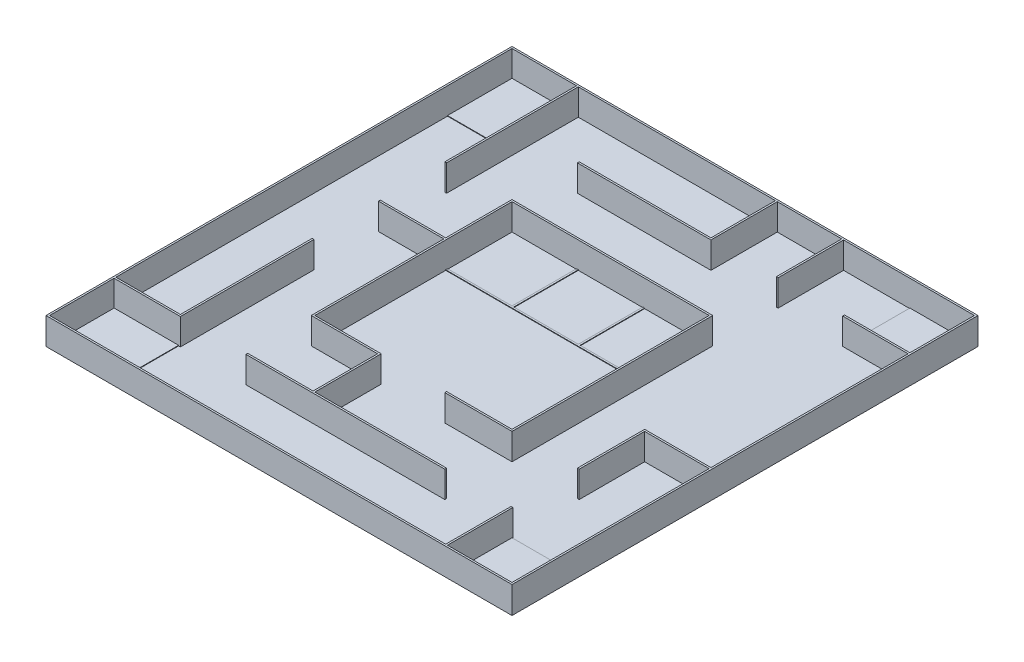
SolidWorks part; units mm, degrees
ref_plane "Front Plane" through (0, 0, 0) normal (0, 0, 1) x (1, 0, 0)
ref_plane "Top Plane" through (0, 0, 0) normal (0, 1, 0) x (1, 0, 0)
ref_plane "Right Plane" through (0, 0, 0) normal (1, 0, 0) x (0, 0, -1)
sketch "Sketch1" plane through (0, 0, 0) normal (0, 1, 0) x (1, 0, 0)
  line L0 (-925, 555) -> (-925, -1290) construction
  line L1 (-1290, -1290) -> (920, -1290)
  line L2 (-1290, -1290) -> (-1290, -930)
  line L3 (-1290, 1290) -> (-930, 1290)
  line L4 (1290, -1290) -> (1290, -190)
  line L5 (-1290, -1290) -> (1290, 1290) construction
  line L6 (-1290, 1290) -> (-930, 930) construction
  line L7 (-555, 1290) -> (-555, -1290) construction
  line L8 (-185, 1290) -> (-185, 930) construction
  line L9 (185, 925) -> (185, -1290) construction
  line L10 (555, 925) -> (555, -1290) construction
  line L11 (925, 1290) -> (925, -185) construction
  line L12 (-925, -925) -> (1290, -925) construction
  line L13 (-1290, 925) -> (-930, 925) construction
  line L14 (-1290, 555) -> (1290, 555) construction
  line L15 (-1290, 185) -> (1290, 185) construction
  line L16 (-1290, -185) -> (925, -185) construction
  line L17 (-1290, -555) -> (1290, -555) construction
  line L18 (-1300, 1300) -> (1300, 1300)
  line L19 (1300, -1300) -> (1300, 1300)
  line L20 (-1300, -1300) -> (1300, -1300)
  line L21 (-1300, -1300) -> (-1300, 1300)
  line L22 (190, 1290) -> (550, 1290)
  line L23 (560, 1290) -> (1290, 1290)
  line L24 (1290, 930) -> (1290, 1290)
  line L25 (1290, -1290) -> (1290, 1290) construction
  line L26 (1290, -180) -> (1290, 920)
  line L27 (185, -555) -> (555, -555)
  line L28 (555, -555) -> (555, -185)
  line L29 (555, -185) -> (555, 185)
  line L30 (555, 185) -> (555, 555)
  line L31 (555, 555) -> (185, 555)
  line L32 (185, 555) -> (-185, 555)
  line L33 (-185, 555) -> (-555, 555)
  line L34 (-555, 555) -> (-555, 185)
  line L35 (-555, 185) -> (-555, -185)
  line L36 (-555, -185) -> (-555, -555)
  line L37 (-555, -555) -> (-185, -555)
  line L38 (-185, -555) -> (-185, -925)
  line L39 (-185, -925) -> (185, -925)
  line L40 (185, -925) -> (555, -925)
  line L41 (-925, 185) -> (-555, 185)
  line L43 (-925, -925) -> (-925, -185)
  line L44 (-555, -925) -> (-185, -925)
  line L45 (925, -555) -> (925, -925) construction
  line L46 (-1290, -920) -> (-1290, 1290)
  line L47 (-1290, -1290) -> (-1290, 1290) construction
  line L48 (-930, 1290) -> (-930, 555)
  line L49 (180, 1290) -> (180, 930)
  line L50 (180, 930) -> (-555, 930)
  line L51 (550, 1290) -> (550, 925)
  line L52 (1290, 930) -> (925, 930)
  line L53 (185, -560) -> (560, -560)
  line L54 (560, -560) -> (560, -185)
  line L55 (560, -185) -> (560, 185)
  line L56 (560, 185) -> (560, 560)
  line L57 (560, 560) -> (185, 560)
  line L58 (185, 560) -> (-185, 560)
  line L59 (-185, 560) -> (-560, 560)
  line L60 (-560, 560) -> (-560, 185)
  line L61 (-560, 185) -> (-560, -185)
  line L62 (-560, -185) -> (-560, -560)
  line L63 (-560, -560) -> (-190, -560)
  line L64 (-190, -560) -> (-190, -925)
  line L65 (-925, 180) -> (-555, 180)
  line L66 (-1290, -930) -> (-920, -930)
  line L67 (-920, -930) -> (-920, -185)
  line L68 (-185, -930) -> (185, -930)
  line L69 (185, -930) -> (555, -930)
  line L70 (-555, -930) -> (-185, -930)
  line L71 (1290, -180) -> (920, -180)
  line L72 (920, -180) -> (920, -555)
  line L73 (930, -1290) -> (930, -925)
  line L74 (-920, 1290) -> (-920, 555)
  line L75 (190, 1290) -> (190, 920)
  line L76 (190, 920) -> (-555, 920)
  line L77 (560, 1290) -> (560, 925)
  line L78 (1290, 920) -> (925, 920)
  line L79 (185, -550) -> (550, -550)
  line L80 (550, -550) -> (550, -185)
  line L81 (550, -185) -> (550, 185)
  line L82 (550, 185) -> (550, 550)
  line L83 (550, 550) -> (185, 550)
  line L84 (185, 550) -> (-185, 550)
  line L85 (-185, 550) -> (-550, 550)
  line L86 (-550, 550) -> (-550, 185)
  line L87 (-550, 185) -> (-550, -185)
  line L88 (-550, -185) -> (-550, -550)
  line L89 (-550, -550) -> (-180, -550)
  line L90 (-180, -550) -> (-180, -925)
  line L91 (-925, 190) -> (-555, 190)
  line L92 (-1290, -920) -> (-930, -920)
  line L93 (-930, -920) -> (-930, -185)
  line L94 (-185, -920) -> (185, -920)
  line L95 (185, -920) -> (555, -920)
  line L96 (-555, -920) -> (-185, -920)
  line L97 (1290, -190) -> (930, -190)
  line L98 (930, -190) -> (930, -555)
  line L99 (920, -1290) -> (920, -925)
  line L101 (-930, 555) -> (-920, 555)
  line L103 (-555, 930) -> (-555, 920)
  line L105 (550, 925) -> (560, 925)
  line L107 (925, 930) -> (925, 920)
  line L108 (185, -560) -> (185, -550)
  line L109 (-560, 185) -> (-550, 185)
  line L110 (-560, 185) -> (-550, 185)
  line L111 (-190, -925) -> (-180, -925)
  line L112 (-925, 180) -> (-925, 190)
  line L113 (-555, 180) -> (-555, 190)
  line L115 (-920, -185) -> (-930, -185)
  line L116 (-185, -930) -> (-185, -920)
  line L117 (555, -930) -> (555, -920)
  line L118 (-555, -930) -> (-555, -920)
  line L119 (-185, -930) -> (-185, -920)
  line L121 (920, -555) -> (930, -555)
  line L123 (930, -925) -> (920, -925)
  line L124 (-920, 1290) -> (180, 1290)
  line L125 (-1290, 1290) -> (1290, 1290) construction
  line L126 (185, 925) -> (925, 925) construction
  line L127 (-925, 925) -> (1290, -1290) construction
  line L128 (-925, 925) -> (-555, 925) construction
  line L129 (930, -1290) -> (1290, -1290)
  line L130 (-185, 925) -> (-185, -1290) construction
  line L131 (-1290, -1290) -> (1290, -1290) construction
  line L133 (-1290, -925) -> (-925, -925) construction
  point P0 (0, 0)
  dimension "D1" = 2580
  dimension "D2" = 2580
  dimension "D3" = 370
  dimension "D4" = 370
  dimension "D5" = 370
  dimension "D6" = 370
  dimension "D7" = 370
  dimension "D8" = 365
  dimension "D9" = 365
  dimension "D10" = 365
  dimension "D11" = 365
  dimension "D12" = 370
  dimension "D13" = 370
  dimension "D14" = 370
  dimension "D15" = 370
  dimension "D16" = 10
  dimension "D17" = 5
  dimension "D18" = 5
extrude "Boss-Extrude1" add sketch "Sketch1" along normal blind 150 contours L64 L96 L38 L37 L36 L35 L65 L61 L62 L63 | L21 L18 L19 L20 | L2 L66 L67 L115 L93 L92 L46 L3 L48 L101 L74 L124 L49 L50 L103 L76 L75 L22 L51 L105 L77 L23 L24 L52 L107 L78 L26 L71 L72 L121 L98 L97 L4 L129 L73 L123 L99 L1 | L56 L57 L58 L59 L60 L109 L86 L85 L84 L83 L82 L81 L80 L79 L108 L53 L54 L55 | L68 L69 L117 L95 L94 L116
sketch "Sketch2" plane through (0, 0, 0) normal (0, 1, 0) x (1, 0, 0)
  line L0 (1300, -1300) -> (1300, 1300) construction
  line L1 (-1300, -1300) -> (1300, -1300) construction
  line L2 (-1300, -1300) -> (-1300, 1300) construction
  line L3 (-1300, 1300) -> (1300, 1300) construction
  line L4 (1300, -1300) -> (1300, 1300)
  line L5 (-1300, -1300) -> (1300, -1300)
  line L6 (-1300, -1300) -> (-1300, 1300)
  line L7 (-1300, 1300) -> (1300, 1300)
extrude "Boss-Extrude2" add sketch "Sketch2" along normal blind 3
sketch "Sketch3" plane through (0, 3, 0) normal (0, 1, 0) x (1, 0, 0)
  line L1 (-1290, 1290) -> (-930, 1290)
  line L2 (-1290, 1290) -> (-1290, 930)
  line L3 (-1290, 930) -> (-930, 930)
  line L4 (-930, 1290) -> (-930, 930)
  dimension "D1" = 360
  dimension "D2" = 360
extrude "Boss-Extrude3" add sketch "Sketch3" along normal blind 3
mirror "Mirror1" about plane through (0, 0, 0) normal (0, 0, 1) of "Boss-Extrude3"
mirror "Mirror2" about plane through (0, 0, 0) normal (1, 0, 0) of "Mirror1", "Boss-Extrude3"
sketch "Sketch5" plane through (0, 3, 0) normal (0, 1, 0) x (1, 0, 0)
  line L0 (-550, 185) -> (550, 185) construction
  line L1 (-550, 550) -> (-550, -550) construction
  line L2 (550, -550) -> (550, 550) construction
  line L3 (-185, 550) -> (-185, 185) construction
  line L4 (550, 550) -> (-550, 550) construction
  line L5 (185, 550) -> (185, 185) construction
  line L6 (550, -550) -> (550, 550)
  line L7 (-550, 550) -> (-550, -550)
  line L8 (550, 550) -> (-550, 550)
  line L9 (-190, 550) -> (-190, 185)
  line L10 (-550, 180) -> (550, 180)
  line L11 (180, 550) -> (180, 185)
  line L12 (-180, 550) -> (-180, 185)
  line L13 (-550, 190) -> (550, 190)
  line L14 (190, 550) -> (190, 185)
  line L15 (-190, 550) -> (-180, 550)
  line L16 (-190, 185) -> (-180, 185)
  line L17 (-550, 180) -> (-550, 190)
  line L18 (550, 180) -> (550, 190)
  line L19 (180, 550) -> (190, 550)
  line L20 (180, 185) -> (190, 185)
  dimension "D1" = 365
  dimension "D2" = 370
  dimension "D3" = 365
  dimension "D4" = 5
  dimension "D5" = 5
extrude "Boss-Extrude4" add sketch "Sketch5" along normal blind 3 contours L13 L18 L10 L17 | L12 L16 L9 L15 | L11 L20 L14 L19
